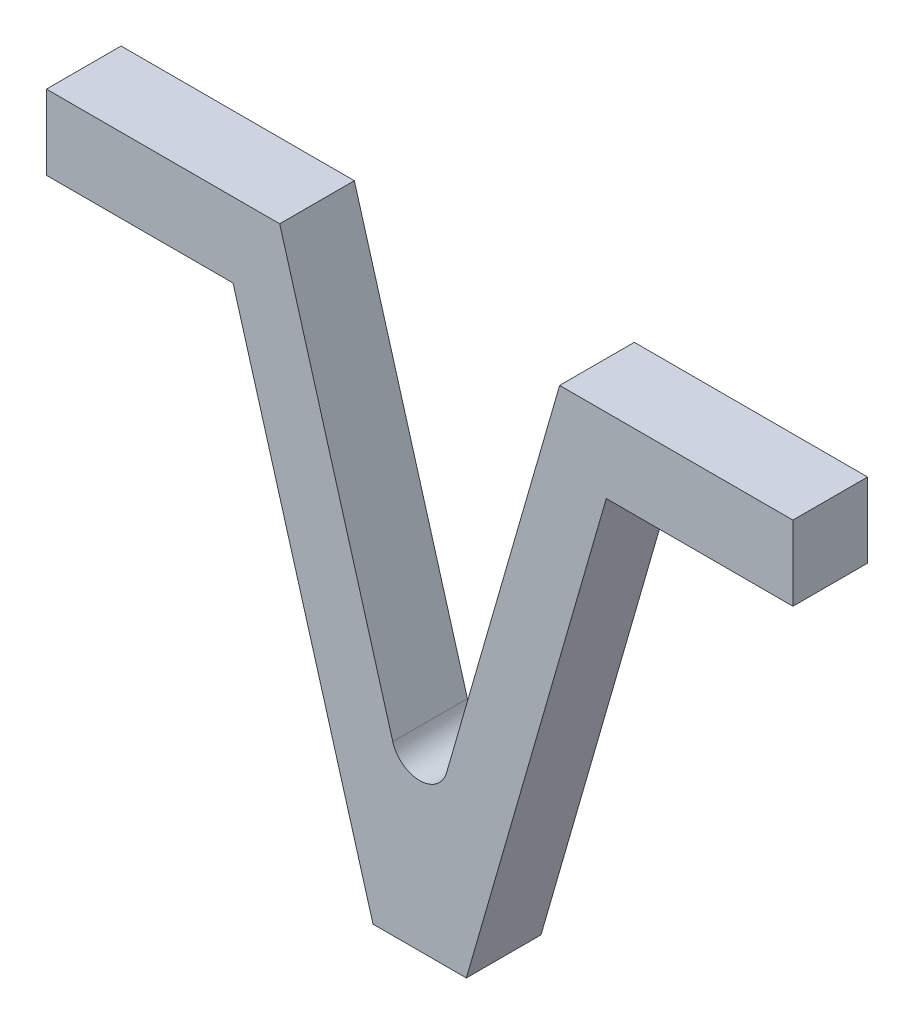
SolidWorks part; units mm, degrees
ref_plane "Plan de face" through (0, 0, 0) normal (0, 0, 1) x (1, 0, 0)
ref_plane "Plan de dessus" through (0, 0, 0) normal (0, 1, 0) x (1, 0, 0)
ref_plane "Plan de droite" through (0, 0, 0) normal (1, 0, 0) x (0, 0, -1)
sketch "Esquisse1" plane through (0, 0, 0) normal (0, 0, 1) x (1, 0, 0)
  line L0 (-40.8614, 48.7635) -> (-15.8614, 48.7635)
  line L1 (-15.8614, 48.7635) -> (-0.8614, -3.2365)
  line L2 (4.1386, -11.2365) -> (-5.8614, -11.2365)
  line L3 (-0.8614, 5.5508) -> (-0.8614, 63.3434) construction
  line L4 (39.1386, 40.7635) -> (39.1386, 48.7635)
  line L5 (39.1386, 48.7635) -> (14.1386, 48.7635)
  line L6 (19.1386, 40.7635) -> (39.1386, 40.7635)
  line L7 (4.1386, -11.2365) -> (19.1386, 40.7635)
  line L8 (14.1386, 48.7635) -> (-0.8614, -3.2365)
  line L9 (-5.8614, -11.2365) -> (-20.8614, 40.7635)
  line L10 (-20.8614, 40.7635) -> (-40.8614, 40.7635)
  line L11 (-40.8614, 40.7635) -> (-40.8614, 48.7635)
  point P14 (-0.8614, -11.2365)
  dimension "D1" = 25
  dimension "D2" = 20
  dimension "D3" = 8
  dimension "D4" = 5
  dimension "D5" = 15
  dimension "D6" = 60
extrude "Boss.-Extru.1" add sketch "Esquisse1" along normal blind 8
fillet "Congé1" radius 3 1 edges at (-0.8614, -3.2365, 4)
